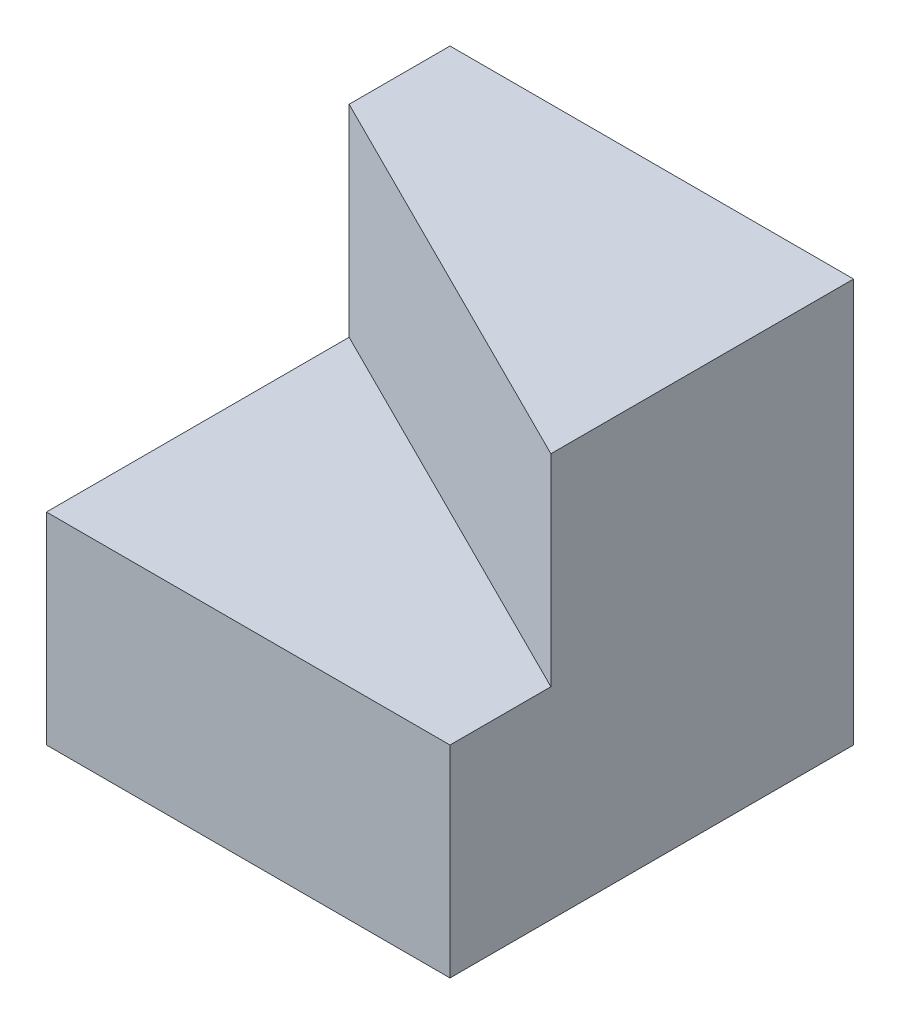
SolidWorks part; units mm, degrees
ref_plane "Front Plane" through (0, 0, 0) normal (0, 0, 1) x (1, 0, 0)
ref_plane "Top Plane" through (0, 0, 0) normal (0, 1, 0) x (1, 0, 0)
ref_plane "Right Plane" through (0, 0, 0) normal (1, 0, 0) x (0, 0, -1)
sketch "Sketch1" plane through (0, 0, 0) normal (0, 0, 1) x (1, 0, 0)
  line L1 (0, 0) -> (40, 0)
  line L2 (0, 0) -> (0, 40)
  line L3 (0, 40) -> (40, 40)
  line L4 (40, 0) -> (40, 40)
  dimension "D1" = 40
  dimension "D2" = 40
extrude "Boss-Extrude1" add sketch "Sketch1" along normal blind 40
sketch "Sketch2" plane through (0, 0, 0) normal (-1, 0, 0) x (0, 0, 1)
  line L1 (0, 40) -> (10, 40)
  line L2 (0, 40) -> (0, 20)
  line L3 (0, 20) -> (10, 20)
  line L4 (10, 40) -> (10, 20)
  dimension "D1" = 10
  dimension "D2" = 20
extrude "Cut-Extrude1" cut sketch "Sketch2" against normal blind 40
sketch "Sketch3" plane through (0, 40, 0) normal (0, 1, 0) x (1, 0, 0)
  line L0 (40, -30) -> (0, -10)
  line L1 (40, -40) -> (40, -10) construction
  line L2 (0, -40) -> (0, -10) construction
  line L3 (0, -10) -> (0, -40)
  line L4 (0, -40) -> (40, -40)
  line L5 (40, -40) -> (40, -30)
  dimension "D1" = 10
  dimension "D2" = 30
extrude "Cut-Extrude2" cut sketch "Sketch3" against normal blind 20
sketch "Sketch4" plane through (0, 0, 0) normal (0, 0, -1) x (-1, 0, 0)
  line L1 (0, 20) -> (-40, 20)
  line L2 (0, 20) -> (0, 40)
  line L3 (0, 40) -> (-40, 40)
  line L4 (-40, 20) -> (-40, 40)
  dimension "D1" = 40
  dimension "D2" = 20
extrude "Boss-Extrude2" add sketch "Sketch4" against normal blind 10
